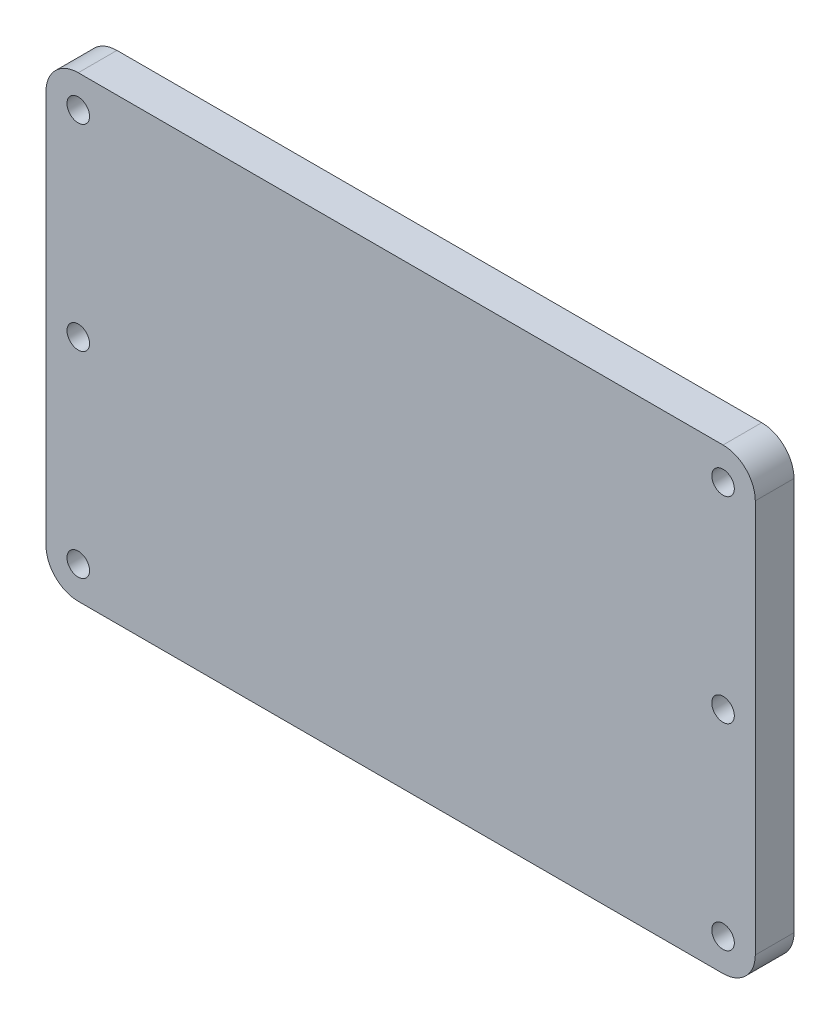
SolidWorks part; units mm, degrees
ref_plane "Plan de face" through (0, 0, 0) normal (0, 0, 1) x (1, 0, 0)
ref_plane "Plan de dessus" through (0, 0, 0) normal (0, 1, 0) x (1, 0, 0)
ref_plane "Plan de droite" through (0, 0, 0) normal (1, 0, 0) x (0, 0, -1)
sketch "Esquisse1" plane through (0, 0, 0) normal (0, 0, 1) x (1, 0, 0)
  line L0 (-50, 30.5) -> (-50, 35.5) construction
  line L1 (-55, 35.5) -> (55, 35.5)
  line L2 (-55, 35.5) -> (-55, -35.5)
  line L3 (-55, -35.5) -> (55, -35.5)
  line L4 (55, 35.5) -> (55, -35.5)
  line L5 (-50, 30.5) -> (-55, 30.5) construction
  line L6 (-55, 0) -> (0, 0) construction
  line L7 (0, 0) -> (0, 35.5) construction
  line L9 (-45, 30) -> (45, 30) construction
  line L10 (-45, 30) -> (-45, -30) construction
  line L11 (-45, -30) -> (45, -30) construction
  line L12 (45, 30) -> (45, -30) construction
  circle A0 centre (-50, 30.5) radius 1.75
  circle A4 centre (50, 30.5) radius 1.75
  circle A5 centre (50, -30.5) radius 1.75
  circle A6 centre (-50, -30.5) radius 1.75
  circle A7 centre (-50, 0) radius 1.75
  circle A8 centre (50, 0) radius 1.75
  point P4 (0, 35.5)
  point P6 (-55, 0)
  point P25 (0, 30)
  point P26 (-45, 0)
  dimension "D3" = 3.5
  dimension "D1" = 110
  dimension "D2" = 71
  dimension "D4" = 5
  dimension "D5" = 60
  dimension "D6" = 90
extrude "Boss.-Extru.1" add sketch "Esquisse1" along normal blind 6
fillet "Congé1" radius 5 4 edges at (-55, -35.5, 3) (55, -35.5, 3) (55, 35.5, 3) (-55, 35.5, 3)
